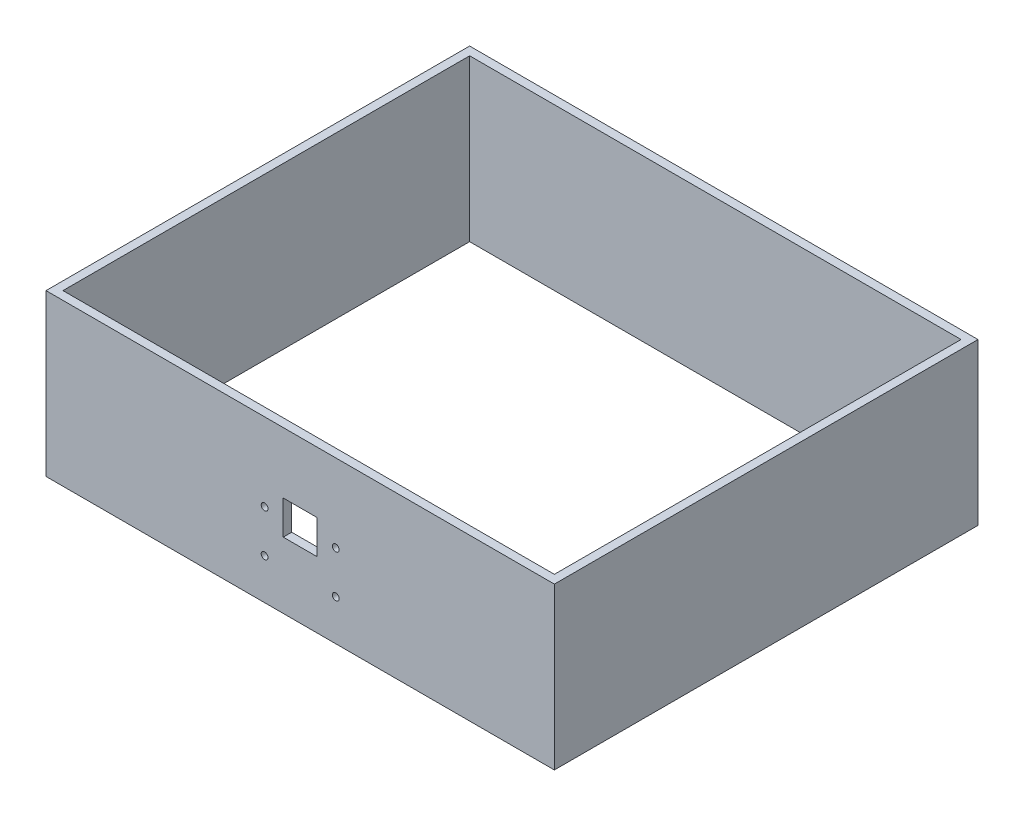
SolidWorks part; units mm, degrees
ref_plane "Front Plane" through (0, 0, 0) normal (0, 0, 1) x (1, 0, 0)
ref_plane "Top Plane" through (0, 0, 0) normal (0, 1, 0) x (1, 0, 0)
ref_plane "Right Plane" through (0, 0, 0) normal (1, 0, 0) x (0, 0, -1)
sketch "Sketch1" plane through (0, 0, 0) normal (0, 1, 0) x (1, 0, 0)
  line L0 (-75, -62.5) -> (-75, 62.5)
  line L1 (0, 0) -> (75, 0) construction
  line L2 (0, -62.5) -> (0, 62.5) construction
  line L3 (-75, 62.5) -> (75, 62.5)
  line L4 (75, -62.5) -> (75, 62.5)
  line L5 (-75, -62.5) -> (-75, 62.5)
  line L6 (75, -62.5) -> (75, 62.5)
  line L7 (-75, -62.5) -> (75, -62.5)
  line L8 (0, 0) -> (-75, 0) construction
  point P10 (-75, 0)
  dimension "D1" = 150
  dimension "D2" = 125
extrude "Boss-Extrude1" add sketch "Sketch1" along normal blind 47.5 contours L0 L7 L4 L3
shell "Shell1" thickness 2.5
sketch "Sketch2" plane through (0, 0, 62.5) normal (0, 0, 1) x (1, 0, 0)
  line L0 (-12.5, 34) -> (12.5, 10) construction
  line L1 (-12.5, 34) -> (12.5, 34) construction
  line L2 (-12.5, 34) -> (-12.5, 10) construction
  line L3 (-12.5, 10) -> (12.5, 10) construction
  line L4 (12.5, 34) -> (12.5, 10) construction
  line L5 (12.5, 34) -> (-12.5, 10) construction
  line L6 (-75, 0) -> (75, 0) construction
  line L7 (0, 34) -> (0, 10) construction
  line L8 (5, 29.5) -> (-5, 19.5) construction
  line L9 (-5, 29.5) -> (5, 29.5)
  line L10 (-5, 29.5) -> (-5, 19.5)
  line L11 (-5, 19.5) -> (5, 19.5)
  line L12 (5, 29.5) -> (5, 19.5)
  line L14 (5, 19.5) -> (-5, 29.5) construction
  circle A0 centre (-10.5, 12) radius 1
  circle A1 centre (-10.5, 24.5) radius 1
  circle A2 centre (10.5, 12) radius 1
  circle A3 centre (10.5, 24.5) radius 1
  point P4 (0, 22)
  point P6 (0, 0)
  point P14 (0, 24.5)
  point P23 (0, 0)
  point P24 (0, 0)
  point P25 (0, 0)
  dimension "D3" = 2
  dimension "D6" = 2
  dimension "D1" = 24
  dimension "D2" = 25
  dimension "D4" = 2
  dimension "D5" = 2
  dimension "D7" = 12.5
  dimension "D8" = 10
  dimension "D9" = 10
  dimension "D10" = 4.5
  dimension "D11" = 10
extrude "Cut-Extrude1" cut sketch "Sketch2" against normal blind 2.5
